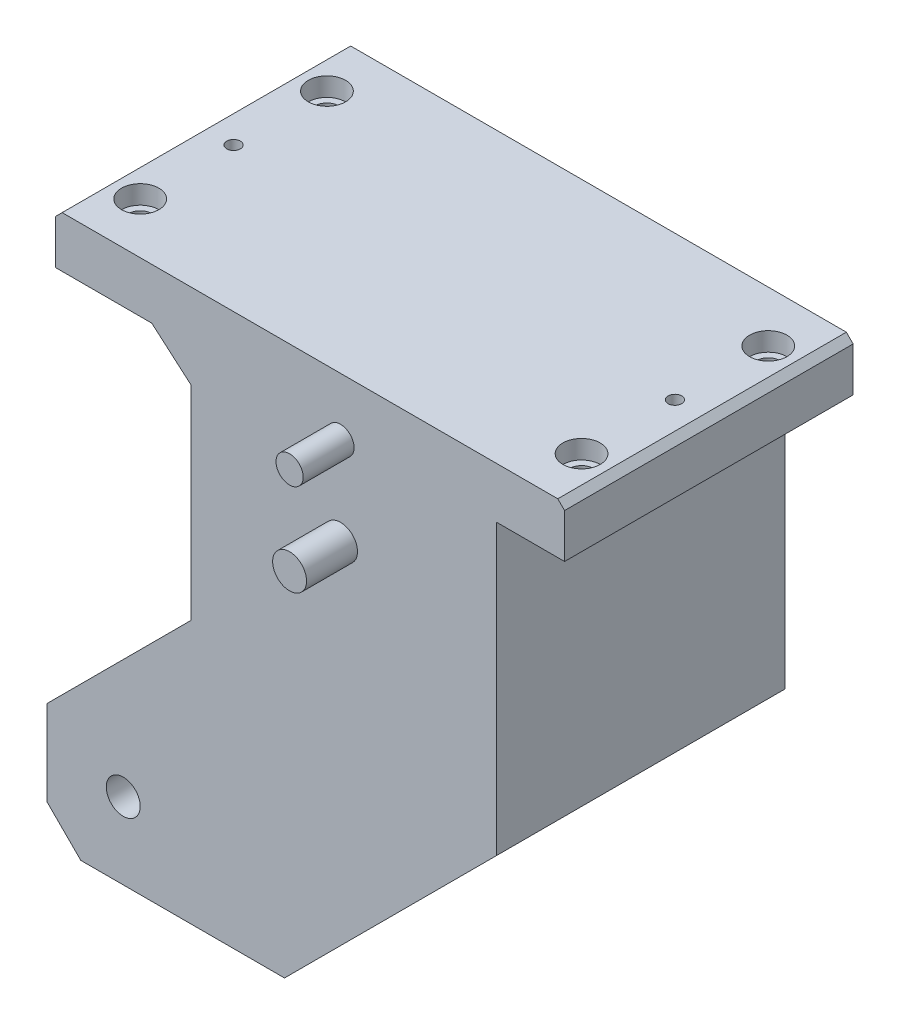
SolidWorks part; units mm, degrees
material "3.0255 (EN-AW 1350A)"
ref_plane "Plan de face" through (0, 0, 0) normal (0, 0, 1) x (1, 0, 0)
ref_plane "Plan de dessus" through (0, 0, 0) normal (0, 1, 0) x (1, 0, 0)
ref_plane "Plan de droite" through (0, 0, 0) normal (1, 0, 0) x (0, 0, -1)
sketch "Esquisse1" plane through (0, 0, 0) normal (0, 0, 1) x (1, 0, 0)
  line L0 (0, 0) -> (0, 69.5749) construction
  line L1 (0, 0) -> (75.4973, 0) construction
  line L2 (-44, 28) -> (-44, -42)
  line L3 (-111.2471, -42) -> (-8.0892, -42) construction
  line L4 (-44, -42) -> (-86.5, -84.5)
  line L5 (-86.5, -84.5) -> (-86.5, -109.5)
  line L6 (-86.5, -109.5) -> (-76.5, -119.5)
  line L7 (-76.5, -119.5) -> (-16.5, -119.5)
  line L8 (-16.5, -119.5) -> (46, -57)
  line L9 (46, -57) -> (46, 28)
  line L10 (46, 28) -> (66, 28)
  line L11 (66, 28) -> (66, 41)
  line L12 (64, 43) -> (-82, 43)
  line L13 (-84, 41) -> (-84, 28)
  line L14 (-84, 28) -> (-55.6092, 28)
  line L15 (-55.6092, 28) -> (-44, 18)
  line L16 (66, 41) -> (64, 43)
  line L17 (-82, 43) -> (-84, 41)
  circle A0 centre (-64, -97) radius 5
  point P12 (66, 43)
  point P16 (-84, 43)
  point P17 (0, 0)
  point P22 (-64, -97)
  dimension "D16" = 10
  dimension "D1" = 70
  dimension "D2" = 45
  dimension "D3" = 42.5
  dimension "D4" = 45
  dimension "D5" = 10
  dimension "D6" = 35
  dimension "D7" = 85
  dimension "D8" = 20
  dimension "D9" = 15
  dimension "D10" = 40.741
  dimension "D11" = 10
  dimension "D12" = 40
  dimension "D13" = 150
  dimension "D14" = 28
  dimension "D15" = 86.5
  dimension "D17" = 22.5
  dimension "D18" = 140
  dimension "D20" = 2
  dimension "D21" = 45
  dimension "D22" = 2
  dimension "D23" = 45
extrude "Boss.-Extru.1" add sketch "Esquisse1" against normal blind 85
sketch "Esquisse3" plane through (0, 0, 0) normal (0, 0, 1) x (1, 0, 0)
  line L2 (46, 28) -> (66, 28) construction
  line L3 (-86.5, -84.5) -> (-86.5, -109.5) construction
  line L5 (64, 43) -> (-82, 43) construction
  circle A0 centre (0, 0) radius 5
  circle A1 centre (0, 26) radius 4
  dimension "D1" = 10
  dimension "D2" = 28
  dimension "D4" = 8
  dimension "D3" = 86.5
  dimension "D5" = 86.5
  dimension "D6" = 17
extrude "Boss.-Extru.2" add sketch "Esquisse3" along normal blind 15
sketch "Esquisse4" plane through (0, 43, 0) normal (0, 1, 0) x (1, 0, 0)
  line L0 (-74, 83.0816) -> (-74, 5.6334) construction
  line L1 (-84, 85) -> (-84, 0) construction
  line L2 (64, 85) -> (-82, 85) construction
  line L3 (64, 0) -> (-82, 0) construction
  line L4 (-9, 0) -> (-9, 85) construction
  circle A0 centre (-74, 70) radius 3.5
  circle A1 centre (-74, 42.5) radius 2
  circle A2 centre (-74, 15) radius 3.5
  dimension "D5" = 4
  dimension "D6" = 7
  dimension "D7" = 7
  dimension "D1" = 10
  dimension "D2" = 15
  dimension "D3" = 42.5
  dimension "D4" = 15
extrude "Enlèv. mat.-Extru.1" cut sketch "Esquisse4" against normal blind 28
sketch "Esquisse6" plane through (0, 43, 0) normal (0, 1, 0) x (1, 0, 0)
  circle A0 centre (-74, 70) radius 5.5
  circle A1 centre (-74, 15) radius 5.5
  dimension "D1" = 11
  dimension "D2" = 11
extrude "Enlèv. mat.-Extru.2" cut sketch "Esquisse6" against normal blind 5.5
ref_plane "Plan1" through (-9, 0, 0) normal (1, 0, 0) x (0, 0, -1)
mirror "Symétrie1" about plane through (-9, 0, 0) normal (1, 0, 0) of "Enlèv. mat.-Extru.2", "Enlèv. mat.-Extru.1"
